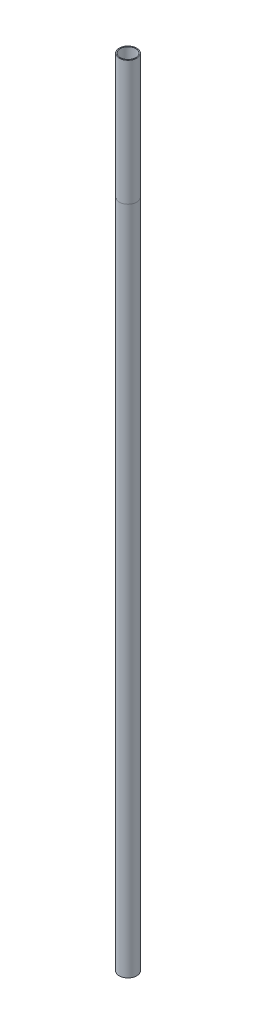
SolidWorks part; units mm, degrees
material "Carbon Fiber"
ref_plane "Front Plane" through (0, 0, 0) normal (0, 0, 1) x (1, 0, 0)
ref_plane "Top Plane" through (0, 0, 0) normal (0, 1, 0) x (1, 0, 0)
ref_plane "Right Plane" through (0, 0, 0) normal (1, 0, 0) x (0, 0, -1)
sketch "Sketch1" plane through (0, 0, 0) normal (0, 1, 0) x (1, 0, 0)
  circle A0 centre (0, 0) radius 14.2875
  circle A1 centre (0, 0) radius 12.7
  dimension "D1" = 1.5875
  dimension "D2" = 25.4
extrude "Boss-Extrude1" add sketch "Sketch1" along normal blind 1295.4
sketch "Sketch2" plane through (0, 0, 0) normal (0, -1, 0) x (1, 0, 0)
  line L1 (6.985, 9.525) -> (-6.985, 9.525)
  line L2 (9.525, 6.985) -> (9.525, -6.985)
  line L3 (6.985, -9.525) -> (-6.985, -9.525)
  line L4 (-9.525, 6.985) -> (-9.525, -6.985)
  line L5 (9.525, 9.525) -> (-9.525, -9.525) construction
  line L6 (9.525, -9.525) -> (-9.525, 9.525) construction
  circle A0 centre (0, 0) radius 12.7 construction
  circle A1 centre (0, 0) radius 12.7
  arc A2 (-9.525, -6.985) -> (-6.985, -9.525) centre (-6.985, -6.985) ccw
  arc A3 (6.985, -9.525) -> (9.525, -6.985) centre (6.985, -6.985) ccw
  arc A4 (9.525, 6.985) -> (6.985, 9.525) centre (6.985, 6.985) ccw
  arc A5 (-6.985, 9.525) -> (-9.525, 6.985) centre (-6.985, 6.985) ccw
  point P3 (0, 0)
  circle M11 centre (0, 0) radius 12.7
  dimension "D1" = 2.54
  dimension "D2" = 19.05
extrude "Boss-Extrude2" add sketch "Sketch2" against normal blind 38.1 contours A5 L1 A4 L2 A3 L3 A2 L4 M11
ref_plane "Plane1" through (0, 1092.2, 0) normal (0, 1, 0) x (1, 0, 0)
split line "Split Line1"
